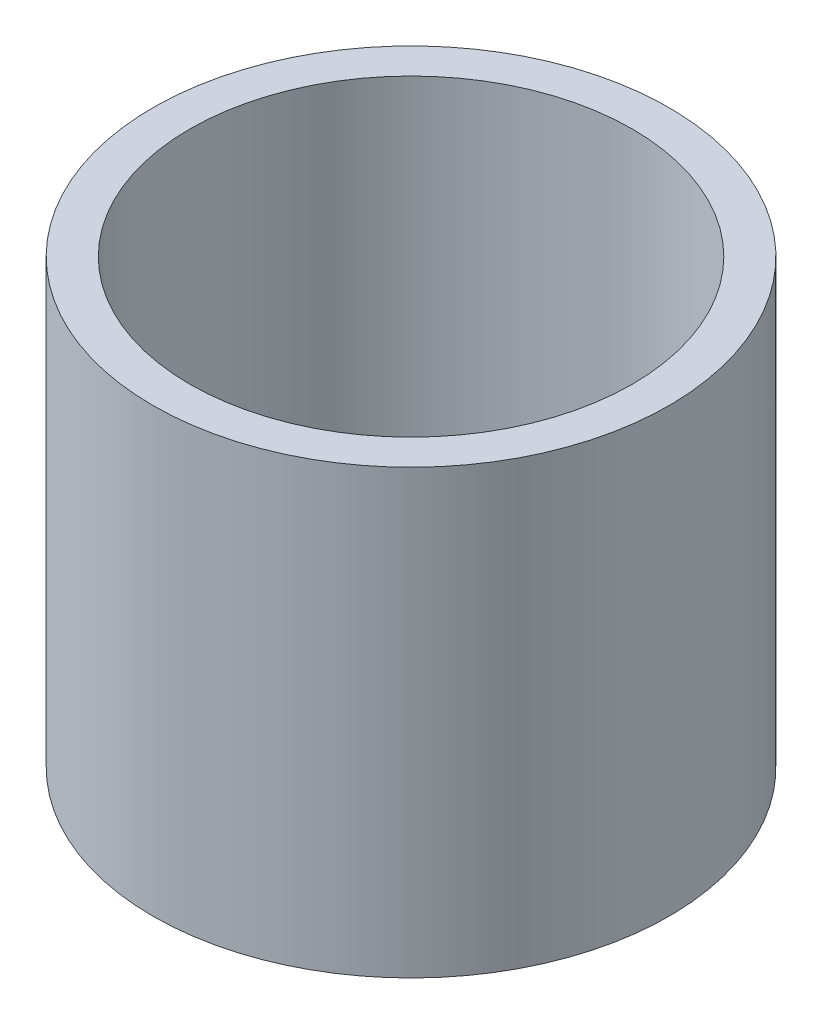
SolidWorks part; units mm, degrees
material "Fireplace Stuff"
ref_plane "Front Plane" through (0, 0, 0) normal (0, 0, 1) x (1, 0, 0)
ref_plane "Top Plane" through (0, 0, 0) normal (0, 1, 0) x (1, 0, 0)
ref_plane "Right Plane" through (0, 0, 0) normal (1, 0, 0) x (0, 0, -1)
sketch "Sketch1" plane through (0, 0, 0) normal (0, 1, 0) x (1, 0, 0)
  circle A0 centre (0, 0) radius 44.45
  circle A1 centre (0, 0) radius 38.1
  dimension "D1" = 76.2
  dimension "D2" = 88.9
extrude "Boss-Extrude1" add sketch "Sketch1" along normal blind 76.2
